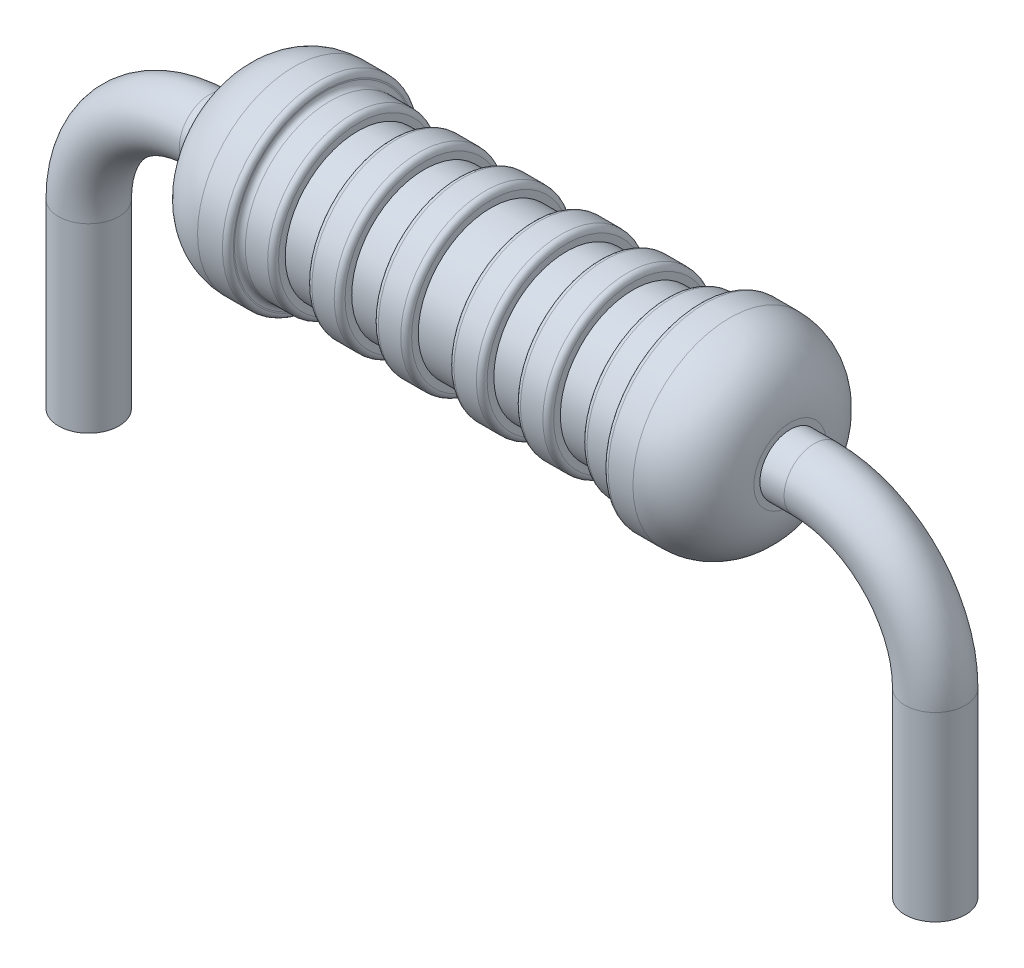
SolidWorks part; units mm, degrees
ref_plane "Front Plane" through (0, 0, 0) normal (0, 0, 1) x (1, 0, 0)
ref_plane "Top Plane" through (0, 0, 0) normal (0, 1, 0) x (1, 0, 0)
ref_plane "Right Plane" through (0, 0, 0) normal (1, 0, 0) x (0, 0, -1)
sketch "Sketch2" plane through (0, 0, 0) normal (0, 1, 0) x (1, 0, 0)
  circle A0 centre (-7, 0) radius 0.5
  point P4 (7, 0)
  dimension "D1" = 1
  dimension "D2" = 7
  dimension "D3" = 7
sketch "Sketch3" plane through (0, 0, 0) normal (0, 0, 1) x (1, 0, 0)
  line L0 (-5, 5) -> (5, 5)
  line L1 (7, 3) -> (7, 0)
  line L2 (-7, 3) -> (-7, 0)
  line L3 (-6.5, 0) -> (-7.5, 0) construction
  arc A0 (7, 3) -> (5, 5) centre (5, 3) ccw
  arc A1 (-7, 3) -> (-5, 5) centre (-5, 3) cw
  point P9 (7, 5)
  point P12 (-7, 5)
  dimension "D3" = 2
  dimension "D1" = 5
sweep "Sweep1" add profiles "Sketch2" path "Sketch3"
sketch "Sketch4" plane through (0, 0, 0) normal (0, 0, 1) x (1, 0, 0)
  line L0 (-4.6, 5) -> (-4.6, 4.4)
  line L1 (-3.6, 3.4) -> (-3.19, 3.4)
  line L2 (-3.1, 3.49) -> (-3.1, 3.51)
  line L3 (-3.01, 3.6) -> (-2.64, 3.6)
  line L4 (-2.55, 3.69) -> (-2.55, 3.8)
  line L5 (-2.55, 3.8) -> (-2, 3.8)
  line L6 (-2, 3.8) -> (-2, 3.69)
  line L7 (-1.91, 3.6) -> (-1.54, 3.6)
  line L8 (-1.45, 3.69) -> (-1.45, 3.8)
  line L9 (-1.45, 3.8) -> (-0.9, 3.8)
  line L10 (-0.9, 3.8) -> (-0.9, 3.69)
  line L11 (-0.81, 3.6) -> (-0.44, 3.6)
  line L12 (-0.35, 3.69) -> (-0.35, 3.8)
  line L13 (-0.35, 3.8) -> (0.35, 3.8)
  line L14 (-5, 5) -> (5, 5) construction
  line L15 (-5, 4.5) -> (-5, 5.5) construction
  line L16 (5, 4.5) -> (5, 5.5) construction
  line L17 (0, 6.2705) -> (0, 3.6371) construction
  line L43 (0.35, 3.69) -> (0.35, 3.8)
  line L44 (0.81, 3.6) -> (0.44, 3.6)
  line L45 (0.9, 3.8) -> (0.9, 3.69)
  line L46 (1.45, 3.8) -> (0.9, 3.8)
  line L47 (1.45, 3.69) -> (1.45, 3.8)
  line L48 (1.91, 3.6) -> (1.54, 3.6)
  line L49 (2, 3.8) -> (2, 3.69)
  line L50 (2.55, 3.8) -> (2, 3.8)
  line L51 (2.55, 3.69) -> (2.55, 3.8)
  line L52 (3.01, 3.6) -> (2.64, 3.6)
  line L53 (3.1, 3.49) -> (3.1, 3.51)
  line L54 (3.6, 3.4) -> (3.19, 3.4)
  line L55 (4.6, 5) -> (4.6, 4.4)
  line L56 (-4.6, 5) -> (4.6, 5)
  arc A0 (-3.19, 3.4) -> (-3.1, 3.49) centre (-3.19, 3.49) ccw
  arc A1 (-0.44, 3.6) -> (-0.35, 3.69) centre (-0.44, 3.69) ccw
  arc A2 (-0.81, 3.6) -> (-0.9, 3.69) centre (-0.81, 3.69) cw
  arc A3 (-1.54, 3.6) -> (-1.45, 3.69) centre (-1.54, 3.69) ccw
  arc A4 (-2, 3.69) -> (-1.91, 3.6) centre (-1.91, 3.69) ccw
  arc A5 (-2.55, 3.69) -> (-2.64, 3.6) centre (-2.64, 3.69) cw
  arc A6 (-3.01, 3.6) -> (-3.1, 3.51) centre (-3.01, 3.51) ccw
  arc A21 (3.01, 3.6) -> (3.1, 3.51) centre (3.01, 3.51) cw
  arc A22 (2.55, 3.69) -> (2.64, 3.6) centre (2.64, 3.69) ccw
  arc A23 (2, 3.69) -> (1.91, 3.6) centre (1.91, 3.69) cw
  arc A24 (1.54, 3.6) -> (1.45, 3.69) centre (1.54, 3.69) cw
  arc A25 (0.81, 3.6) -> (0.9, 3.69) centre (0.81, 3.69) ccw
  arc A26 (0.44, 3.6) -> (0.35, 3.69) centre (0.44, 3.69) cw
  arc A27 (3.19, 3.4) -> (3.1, 3.49) centre (3.19, 3.49) cw
  arc A28 (4.6, 4.4) -> (3.6, 3.4) centre (3.6, 4.4) cw
  arc A30 (-3.6, 3.4) -> (-4.6, 4.4) centre (-3.6, 4.4) cw
  point P28 (-3.1, 3.4)
  point P31 (-0.35, 3.6)
  point P34 (-0.9, 3.6)
  point P37 (-1.45, 3.6)
  point P40 (-2, 3.6)
  point P43 (-2.55, 3.6)
  point P46 (-3.1, 3.6)
  point P130 (0, 3.8)
  point P142 (3.1, 3.6)
  point P143 (2.55, 3.6)
  point P144 (2, 3.6)
  point P145 (1.45, 3.6)
  point P146 (0.9, 3.6)
  point P147 (0.35, 3.6)
  point P148 (3.1, 3.4)
  point P151 (4.6, 3.4)
  point P157 (-4.6, 3.4)
  dimension "D11" = 0.09
  dimension "D12" = 1
  dimension "D2" = 4.6
  dimension "D3" = 1.5
  dimension "D4" = 0.55
  dimension "D5" = 0.55
  dimension "D6" = 0.55
  dimension "D7" = 0.55
  dimension "D8" = 0.55
  dimension "D9" = 0.2
  dimension "D10" = 0.2
  dimension "D13" = 1.6
  dimension "D14" = 0.6
  dimension "D15" = 0.6
revolve "Revolve1" add sketch "Sketch4" angle 360 about L56
